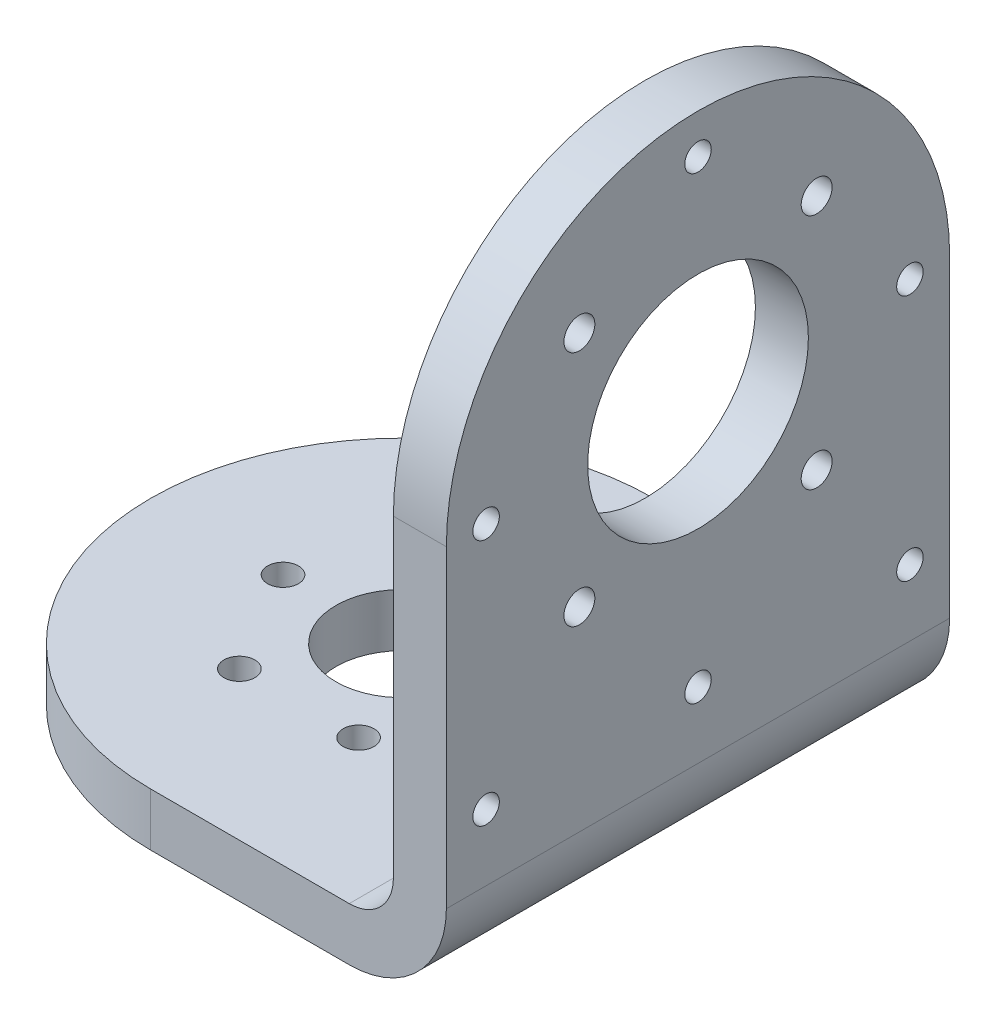
SolidWorks part; units mm, degrees
material "AISI 304"
ref_plane "前视基准面" through (0, 0, 0) normal (0, 0, 1) x (1, 0, 0)
ref_plane "上视基准面" through (0, 0, 0) normal (0, 1, 0) x (1, 0, 0)
ref_plane "右视基准面" through (0, 0, 0) normal (1, 0, 0) x (0, 0, -1)
sketch "草图1" plane through (0, 0, 0) normal (0, 1, 0) x (1, 0, 0)
  line L0 (0, -28.5) -> (33.5, -28.5)
  line L1 (0, 28.5) -> (33.5, 28.5)
  line L2 (33.5, 28.5) -> (33.5, -28.5)
  line L3 (28.5, 28.5) -> (28.5, -28.5)
  circle A0 centre (0, 0) radius 28.5
  dimension "D1" = 57
  dimension "D2" = 28.5
  dimension "D3" = 5
extrude "凸台-拉伸1" add sketch "草图1" along normal blind 6 contours A0 | A0 L0 L3 L1 | L1 L3 L0 L2 | A0 L3 L1
sketch "草图3" plane through (33.5, 0, 0) normal (1, 0, 0) x (0, 0, -1)
  line L0 (0, 57.6553) -> (0, -23.6227) construction
  line L1 (28.5, 0) -> (-28.5, 0) construction
  line L4 (-28.5, 6) -> (-28.5, 46.5)
  line L5 (28.5, 6) -> (28.5, 46.5)
  circle A0 centre (0, 46.5) radius 28.5
  line M5 (28.5, 6) -> (-28.5, 6)
  dimension "D1" = 57
  dimension "D2" = 46.5
extrude "凸台-拉伸2" add sketch "草图3" against normal blind 6 contours A0 L5 M5 | A0 L4 M5 | L0 A0 | A0 L0
sketch "草图4" plane through (0, 6, 0) normal (0, 1, 0) x (1, 0, 0)
  circle A0 centre (0, 0) radius 13.5
  circle A1 centre (-13.5, 0) radius 1.75
  circle A2 centre (-6.75, 11.6913) radius 1.75
  circle A3 centre (6.75, 11.6913) radius 1.75
  circle A4 centre (13.5, 0) radius 1.75
  circle A5 centre (6.75, -11.6913) radius 1.75
  circle A6 centre (-6.75, -11.6913) radius 1.75
  point P17 (0, 0)
  dimension "D1" = 27
  dimension "D2" = 3.5
  dimension "D3" = 6
extrude "切除-拉伸1" cut sketch "草图4" against normal blind 16 contours A0 A2 | A0 A2 | A0 A3 | A0 A3 | A0 A4 | A0 A4 | A0 A5 | A0 A5 | A0 A6 | A0 A6 | A0 A1 | A0 A1
sketch "草图6" plane through (33.5, 0, 0) normal (1, 0, 0) x (0, 0, -1)
  line L0 (0, 50) -> (0, 69) construction
  line L1 (0, 46.5) -> (-13.435, 59.935) construction
  circle A0 centre (0, 46.5) radius 19 construction
  circle A1 centre (-13.435, 59.935) radius 1.75
  circle A2 centre (13.435, 59.935) radius 1.75
  circle A3 centre (13.435, 33.065) radius 1.75
  circle A4 centre (-13.435, 33.065) radius 1.75
  point P18 (0, 46.5)
  dimension "D1" = 38
  dimension "D3" = 3.5
  dimension "D2" = 45
  dimension "D4" = 4
extrude "切除-拉伸2" cut sketch "草图6" against normal blind 16
fillet "圆角1" radius 5 1 edges at (27.5, 6, 0)
fillet "圆角2" radius 11 1 edges at (33.5, 0, 0)
sketch "草图7" plane through (33.5, 0, 0) normal (1, 0, 0) x (0, 0, -1)
  line L0 (-24, 46.5) -> (-24, 18.5) construction
  line L1 (-24, 18.5) -> (24, 18.5) construction
  line L2 (24, 46.5) -> (24, 18.5) construction
  circle A0 centre (0, 46.5) radius 24 construction
  circle A1 centre (0, 70.5) radius 1.5
  circle A2 centre (-24, 46.5) radius 1.5
  circle A3 centre (24, 46.5) radius 1.5
  circle A4 centre (-24, 18.5) radius 1.5
  circle A5 centre (24, 18.5) radius 1.5
  circle A6 centre (0, 18.5) radius 1.5
  circle A7 centre (0, 46.5) radius 12.5
  dimension "D1" = 48
  dimension "D2" = 3
  dimension "D3" = 3
  dimension "D4" = 3
  dimension "D5" = 3
  dimension "D6" = 3
  dimension "D7" = 28
  dimension "D8" = 3
  dimension "D9" = 25
extrude "切除-拉伸3" cut sketch "草图7" against normal blind 10
sketch "草图8" plane through (0, 6, 0) normal (0, 1, 0) x (1, 0, 0)
  circle A0 centre (0, 0) radius 7.5
  dimension "D1" = 15
extrude "切除-拉伸4" cut sketch "草图8" against normal blind 10
sketch "草图9" plane through (0, 6, 0) normal (0, 1, 0) x (1, 0, 0)
  circle A0 centre (-6.75, 11.6913) radius 3
  circle A1 centre (6.75, 11.6913) radius 3
  circle A2 centre (13.5, 0) radius 3
  circle A3 centre (6.75, -11.6913) radius 3
  circle A4 centre (-6.75, -11.6913) radius 3
  circle A5 centre (-13.5, 0) radius 3
  dimension "D1" = 6
  dimension "D2" = 6
  dimension "D3" = 6
  dimension "D4" = 6
  dimension "D5" = 6
  dimension "D6" = 6
extrude "切除-拉伸5" [suppressed] cut sketch "草图9" against normal blind 3
sketch "草图10" plane through (33.5, 0, 0) normal (1, 0, 0) x (0, 0, -1)
  circle A0 centre (13.435, 59.935) radius 3
  circle A1 centre (13.435, 33.065) radius 3
  circle A3 centre (-13.435, 33.065) radius 3
  circle A4 centre (-13.435, 59.935) radius 3
  dimension "D1" = 6
  dimension "D2" = 6
  dimension "D3" = 6
  dimension "D4" = 6
extrude "切除-拉伸6" [suppressed] cut sketch "草图10" against normal blind 3
